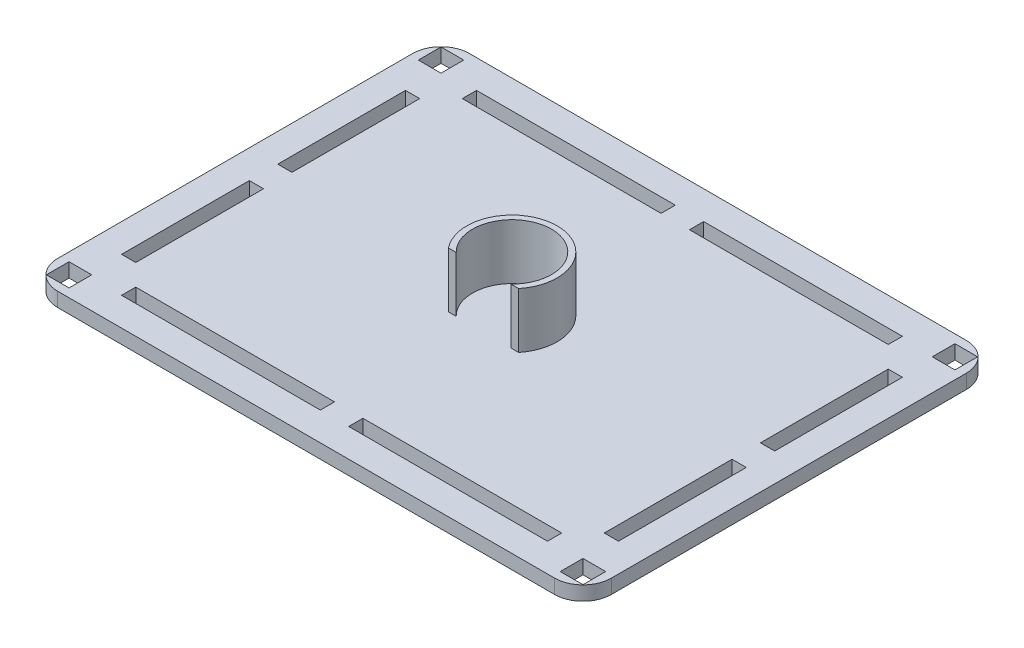
SolidWorks part; units mm, degrees
ref_plane "Front Plane" through (0, 0, 0) normal (0, 0, 1) x (1, 0, 0)
ref_plane "Top Plane" through (0, 0, 0) normal (0, 1, 0) x (1, 0, 0)
ref_plane "Right Plane" through (0, 0, 0) normal (1, 0, 0) x (0, 0, -1)
sketch "Sketch4" plane through (0, 0, 0) normal (0, 1, 0) x (1, 0, 0)
  line L0 (-97.5, 72.5) -> (97.5, 72.5)
  line L1 (97.5, 72.5) -> (97.5, -72.5)
  line L2 (-97.5, -72.5) -> (97.5, -72.5)
  line L3 (-97.5, 72.5) -> (-97.5, -72.5)
  line L4 (-97.5, 72.5) -> (97.5, 72.5)
  line L5 (-97.5, 72.5) -> (-97.5, -72.5)
  line L6 (-97.5, -72.5) -> (97.5, -72.5)
  line L7 (97.5, 72.5) -> (97.5, -72.5)
  line L8 (-97.5, 72.5) -> (97.5, -72.5)
  line L9 (97.5, 72.5) -> (-97.5, -72.5)
  point P4 (0, 0)
  dimension "D1" = 145
  dimension "D2" = 195
extrude "Boss-Extrude2" add sketch "Sketch4" along normal blind 5 contours L9 L8 L3 | L8 L9 L2 | L9 L0 L8 | L1 L9 L8
sketch "Sketch5" plane through (0, 5, 0) normal (0, 1, 0) x (1, 0, 0)
  line L4 (-87.5, 62.5) -> (-87.5, -62.5)
  line L5 (-87.5, -62.5) -> (87.5, -62.5)
  line L6 (87.5, 62.5) -> (87.5, -62.5)
  line L7 (-87.5, 62.5) -> (87.5, 62.5)
  line L8 (-82.5, 57.5) -> (82.5, 57.5)
  line L9 (82.5, 57.5) -> (82.5, -57.5)
  line L10 (-82.5, -57.5) -> (82.5, -57.5)
  line L11 (-82.5, 57.5) -> (-82.5, -57.5)
  line L12 (-82.5, 57.5) -> (-87.5, 57.5)
  line L13 (-87.5, 57.5) -> (82.5, 57.5)
  line L14 (82.5, 57.5) -> (87.5, 57.5)
  line L15 (82.5, -57.5) -> (87.5, -57.5)
  line L16 (-82.5, -57.5) -> (-87.5, -57.5)
  line L17 (-82.5, 57.5) -> (-82.5, 62.5)
  line L18 (82.5, 57.5) -> (82.5, 62.5)
  line L19 (82.5, -57.5) -> (82.5, -62.5)
  line L20 (-82.5, -57.5) -> (-82.5, -62.5)
  line L21 (-87.5, -50) -> (87.5, -50)
  line L22 (-87.5, 50) -> (87.5, 50)
  line L23 (-75, 62.5) -> (-75, -62.5)
  line L24 (75, 62.5) -> (75, -62.5)
  line L25 (-87.5, -5) -> (87.5, -5)
  line L26 (-87.5, -5) -> (-87.5, 5)
  line L27 (-87.5, 5) -> (87.5, 5)
  line L28 (87.5, -5) -> (87.5, 5)
  line L29 (-87.5, -5) -> (87.5, 5) construction
  line L30 (-87.5, 5) -> (87.5, -5) construction
  line L31 (5, -62.5) -> (-5, -62.5)
  line L32 (5, -62.5) -> (5, 62.5)
  line L33 (5, 62.5) -> (-5, 62.5)
  line L34 (-5, -62.5) -> (-5, 62.5)
  line L35 (5, -62.5) -> (-5, 62.5) construction
  line L36 (5, 62.5) -> (-5, -62.5) construction
  point P28 (0, 0)
  point P33 (0, 0)
extrude "Cut-Extrude5" cut sketch "Sketch5" against normal through all contours L4 L27 L11 L22 | L25 L4 L21 L11 | L5 L34 L10 L23 | L32 L5 L24 L10 | L25 L9 L21 L6 | L9 L27 L6 L22 | L32 L8 L24 L7 | L13 L34 L7 L23
sketch "Sketch6" plane through (0, 5, 0) normal (0, 1, 0) x (1, 0, 0)
  line L0 (-12.3616, -10) -> (12.3616, -10)
  line L1 (-12.3616, -10) -> (-12.3616, -11)
  line L2 (-12.3616, -11) -> (12.3616, -11)
  line L3 (12.3616, -10) -> (12.3616, -11)
  circle A0 centre (0, 0) radius 13.9
  circle A1 centre (0, 0) radius 15.9
  dimension "D1" = 2
  dimension "D2" = 27.8
extrude "Boss-Extrude3" add sketch "Sketch6" along normal blind 19.5 contours L0 A1 A0
fillet "Fillet1" radius 10 4 edges at (97.5, 2.5, -72.5) (97.5, 2.5, 72.5) (-97.5, 2.5, -72.5) (-97.5, 2.5, 72.5)
sketch "Sketch7" plane through (0, 5, 0) normal (0, 1, 0) x (1, 0, 0)
  line L0 (-94.5, -61.5) -> (-86.5, -61.5)
  line L1 (-94.5, -61.5) -> (-94.5, -69.5)
  line L2 (-94.5, -69.5) -> (-86.5, -69.5)
  line L3 (-86.5, -61.5) -> (-86.5, -69.5)
  line L4 (94.5, -61.5) -> (94.5, -69.5)
  line L5 (94.5, -69.5) -> (86.5, -69.5)
  line L6 (86.5, -61.5) -> (86.5, -69.5)
  line L7 (94.5, -61.5) -> (86.5, -61.5)
  line L8 (94.5, 61.5) -> (86.5, 61.5)
  line L9 (94.5, 61.5) -> (94.5, 69.5)
  line L10 (94.5, 69.5) -> (86.5, 69.5)
  line L11 (86.5, 61.5) -> (86.5, 69.5)
  line L12 (-86.5, 61.5) -> (-86.5, 69.5)
  line L13 (-94.5, 69.5) -> (-86.5, 69.5)
  line L14 (-94.5, 61.5) -> (-94.5, 69.5)
  line L15 (-94.5, 61.5) -> (-86.5, 61.5)
  line L16 (94.5, 69.5) -> (-94.5, -69.5)
  line L17 (-94.5, 69.5) -> (94.5, 69.5)
  line L18 (-94.5, 69.5) -> (-94.5, -69.5)
  line L19 (-94.5, -69.5) -> (94.5, -69.5)
  line L20 (94.5, 69.5) -> (94.5, -69.5)
  line L21 (-94.5, 69.5) -> (94.5, -69.5)
  point P16 (0, 0)
extrude "Cut-Extrude6" cut sketch "Sketch7" against normal up to vertex (5 mm away) contours L13 L21 L12 | L21 L14 L15 L12 | L16 L3 L0 L1 | L3 L16 L2 | L21 L6 L5 | L6 L21 L4 L7 | L16 L10 L11 | L9 L16 L11 L8 up to point (0, 0, 0)
